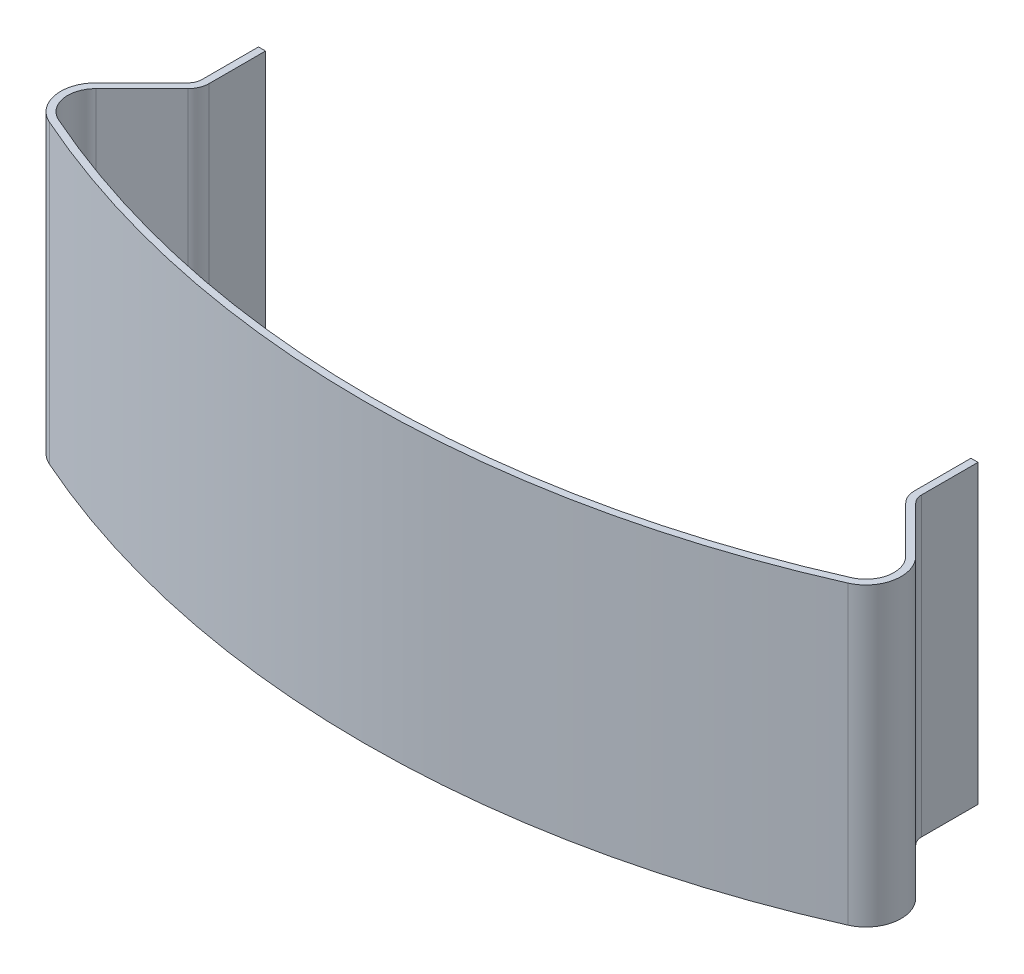
SolidWorks part; units mm, degrees
material "1060 Alloy"
ref_plane "Front Plane" through (0, 0, 0) normal (0, 0, 1) x (1, 0, 0)
ref_plane "Top Plane" through (0, 0, 0) normal (0, 1, 0) x (1, 0, 0)
ref_plane "Right Plane" through (0, 0, 0) normal (1, 0, 0) x (0, 0, -1)
sketch "Sketch1" plane through (0, 0, 0) normal (0, 1, 0) x (1, 0, 0)
  line L0 (-58.1123, -119.9407) -> (-51.5858, -113.4142)
  line L1 (-51, -112) -> (-51, -104)
  line L2 (-51, -104) -> (-50, -104)
  line L3 (-50, -104) -> (-50, -112)
  line L4 (-50.8787, -114.1213) -> (-57.4052, -120.6478)
  line L5 (57.4052, -120.6478) -> (50.8787, -114.1213)
  line L6 (58.1123, -119.9407) -> (51.5858, -113.4142)
  line L7 (51, -112) -> (51, -104)
  line L8 (51, -104) -> (50, -104)
  line L9 (50, -104) -> (50, -112)
  arc A0 (-56.5981, -128.0494) -> (56.5981, -128.0494) centre (0, 0) ccw
  arc A1 (-56.5981, -128.0494) -> (-58.1123, -119.9407) centre (-54.5767, -123.4762) cw
  arc A2 (-51.5858, -113.4142) -> (-51, -112) centre (-53, -112) ccw
  arc A3 (-50, -112) -> (-50.8787, -114.1213) centre (-53, -112) cw
  arc A4 (-57.4052, -120.6478) -> (-56.1938, -127.1348) centre (-54.5767, -123.4762) ccw
  arc A5 (-56.1938, -127.1348) -> (56.1938, -127.1348) centre (0, 0) ccw
  arc A6 (56.5981, -128.0494) -> (58.1123, -119.9407) centre (54.5767, -123.4762) ccw
  arc A7 (56.1938, -127.1348) -> (57.4052, -120.6478) centre (54.5767, -123.4762) ccw
  arc A8 (50.8787, -114.1213) -> (50, -112) centre (53, -112) cw
  arc A9 (51.5858, -113.4142) -> (51, -112) centre (53, -112) cw
  dimension "D1" = 140
  dimension "D4" = 5
  dimension "D5" = 3
  dimension "D9" = 135
  dimension "D2" = 1
  dimension "D3" = 100
  dimension "D6" = 104
  dimension "D7" = 50
  dimension "D8" = 8
extrude "Boss-Extrude1" add sketch "Sketch1" along normal blind 42
